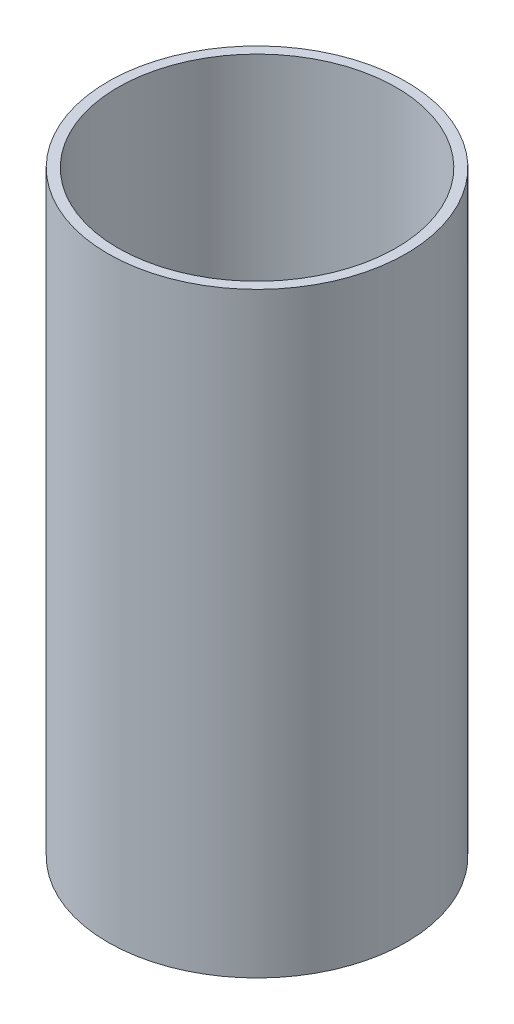
SolidWorks part; units mm, degrees
ref_plane "前视基准面" through (0, 0, 0) normal (0, 0, 1) x (1, 0, 0)
ref_plane "上视基准面" through (0, 0, 0) normal (0, 1, 0) x (1, 0, 0)
ref_plane "右视基准面" through (0, 0, 0) normal (1, 0, 0) x (0, 0, -1)
sketch "草图1" plane through (0, 0, 0) normal (0, 1, 0) x (1, 0, 0)
  circle A0 centre (0, 0) radius 3
  dimension "D1" = 6
extrude "凸台-拉伸1" add sketch "草图1" along normal blind 12
sketch "草图2" plane through (0, 12, 0) normal (0, 1, 0) x (1, 0, 0)
  circle A0 centre (0, 0) radius 2.8
  circle A1 centre (0, 0) radius 3 construction
  dimension "D1" = 0.2
extrude "切除-拉伸1" cut sketch "草图2" against normal up to surface (12 mm away) up to face at (0, 0, 3)
